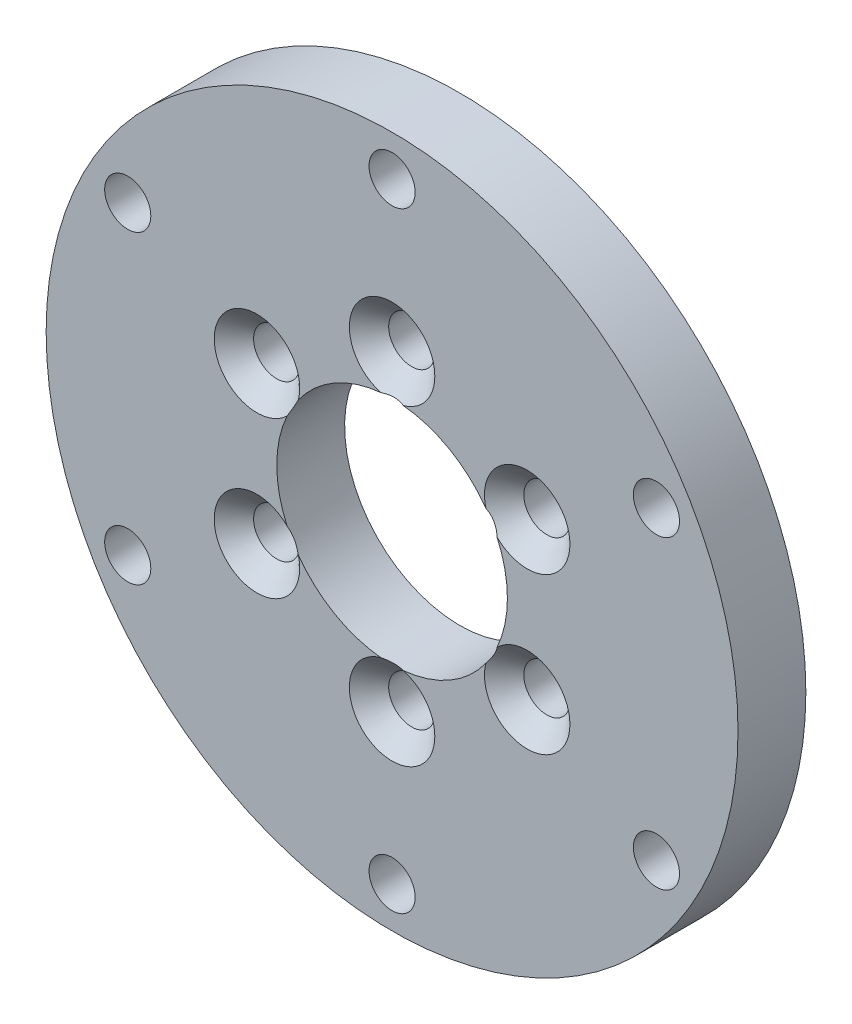
SolidWorks part; units mm, degrees
ref_plane "Front Plane" through (0, 0, 0) normal (0, 0, 1) x (1, 0, 0)
ref_plane "Top Plane" through (0, 0, 0) normal (0, 1, 0) x (1, 0, 0)
ref_plane "Right Plane" through (0, 0, 0) normal (1, 0, 0) x (0, 0, -1)
sketch "Sketch1" plane through (0, 0, 0) normal (0, 0, 1) x (1, 0, 0)
  circle A0 centre (0, 0) radius 22.5 construction
  circle A1 centre (0, 0) radius 11.5 construction
  circle A2 centre (0, 0) radius 25.5
  circle A3 centre (0, 0) radius 8.5
  dimension "D1" = 23
  dimension "D2" = 45
  dimension "D3" = 3
  dimension "D4" = 3
extrude "Boss-Extrude1" add sketch "Sketch1" along normal blind 5
hole_wizard "M3 Clearance Hole1" positions "Sketch2" profile "Sketch3" hole size "M3" standard "ISO"
sketch "Sketch2" plane through (0, 0, 5) normal (0, 0, 1) x (1, 0, 0)
  circle A0 centre (0, 0) radius 22.5 construction
  point P0 (0, 22.5)
sketch "Sketch3" plane through (0, 22.5, 5) normal (1, 0, 0) x (0, -1, 0)
  line L0 (0, 0) -> (0, 11.0215)
  line L1 (0, 11.0215) -> (1.7, 10)
  line L2 (1.7, 10) -> (1.7, 0)
  line L5 (1.7, 0) -> (0, 0)
  line L10 (0, 11.0215) -> (-1.7, 10) construction
  line L11 (0, -6.35) -> (0, 107.95) construction
  dimension "Hole Dia." = 3.4
  dimension "Hole Depth" = 10
  dimension "Drill Angle" = 118
hole_wizard "CSK for M3 Countersunk Flat Head Screw3" positions "Sketch4" profile "Sketch5" countersink size "M3" standard "ISO"
sketch "Sketch4" plane through (0, 0, 5) normal (0, 0, 1) x (1, 0, 0)
  circle A0 centre (0, 0) radius 11.5 construction
  point P0 (0, 11.5)
sketch "Sketch5" plane through (0, 11.5, 5) normal (1, 0, 0) x (0, -1, 0)
  line L0 (0, 0) -> (0, 11.0215)
  line L1 (0, 11.0215) -> (1.7, 10)
  line L2 (1.7, 10) -> (1.7, 1.45)
  line L3 (1.7, 1.45) -> (3.15, 0)
  line L5 (3.15, 0) -> (0, 0)
  line L6 (-1.7, 1.45) -> (-3.15, 0) construction
  line L10 (0, 11.0215) -> (-1.7, 10) construction
  line L11 (0, -6.35) -> (0, 107.95) construction
  dimension "Hole Dia." = 3.4
  dimension "Hole Depth" = 10
  dimension "Near C'Sink Dia." = 6.3
  dimension "Near C'Sink Angle" = 90
  dimension "Drill Angle" = 118
pattern_circular "CirPattern1" count 6 over 360 about axis through (0, 0, 0) along (0, 0, 1) of "CSK for M3 Countersunk Flat Head Screw3", "M3 Clearance Hole1"
